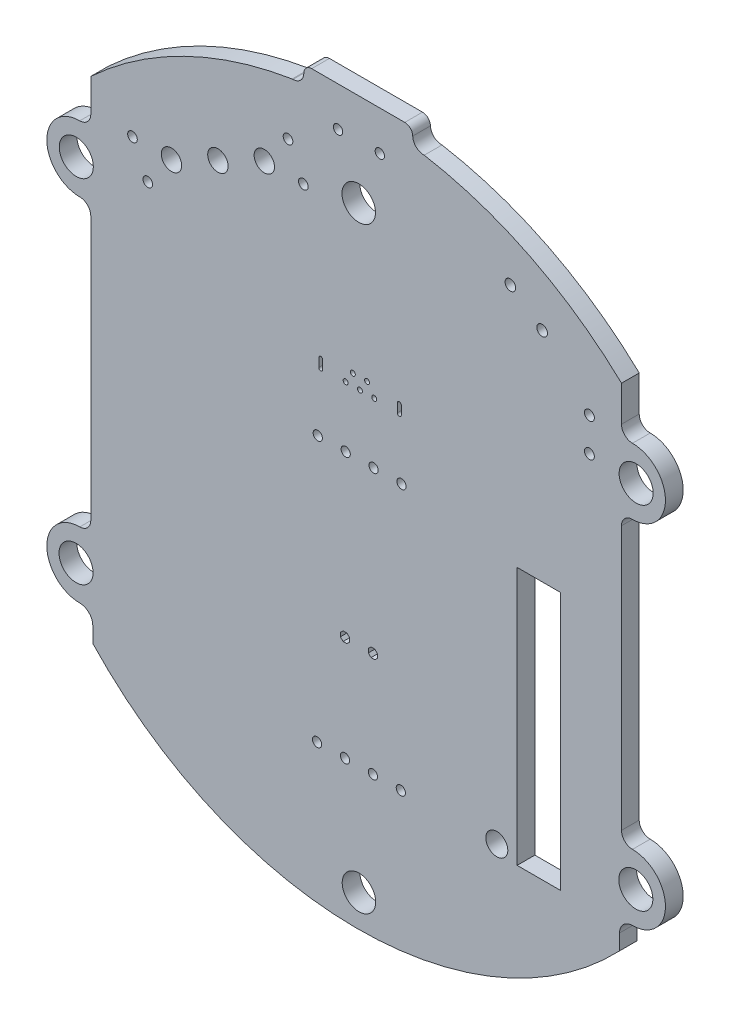
SolidWorks part; units mm, degrees
ref_plane "Front Plane" through (0, 0, 0) normal (0, 0, 1) x (1, 0, 0)
ref_plane "Top Plane" through (0, 0, 0) normal (0, 1, 0) x (1, 0, 0)
ref_plane "Right Plane" through (0, 0, 0) normal (1, 0, 0) x (0, 0, -1)
sketch "Model" plane through (0, 0, 0) normal (0, 0, 1) x (1, 0, 0)
  line L1 (-3.0387, 14.0018) -> (-3.0387, 13.2168) construction
  line L2 (-2.8588, 14.0018) -> (-2.8588, 13.2168)
  line L3 (4.1113, 14.0018) -> (4.1113, 13.2168) construction
  line L4 (4.2912, 14.0018) -> (4.2912, 13.2168)
  line L5 (3.9314, 14.0018) -> (3.9314, 13.2168)
  line L6 (-3.2186, 14.0018) -> (-3.2186, 13.2168)
  line L18 (2.1284, -6.6742) -> (2.1284, -7.0215)
  line L19 (2.1284, -7.0215) -> (1.883, -7.2669)
  line L20 (1.883, -7.2669) -> (1.5356, -7.2669)
  line L21 (1.5356, -7.2669) -> (1.2902, -7.0215)
  line L22 (1.2902, -7.0215) -> (1.2902, -6.6742)
  line L23 (1.2902, -6.6742) -> (1.5356, -6.4287)
  line L24 (1.5356, -6.4287) -> (1.883, -6.4287)
  line L25 (1.883, -6.4287) -> (2.1284, -6.6742)
  line L26 (2.1284, -6.6742) -> (2.1284, -7.0215)
  line L27 (2.1284, -6.6742) -> (2.1284, -7.0215)
  line L28 (2.1284, -7.0215) -> (1.883, -7.2669)
  line L29 (1.883, -7.2669) -> (1.5356, -7.2669)
  line L30 (1.5356, -7.2669) -> (1.2902, -7.0215)
  line L31 (1.2902, -7.0215) -> (1.2902, -6.6742)
  line L32 (1.2902, -6.6742) -> (1.5356, -6.4287)
  line L33 (1.5356, -6.4287) -> (1.883, -6.4287)
  line L34 (1.883, -6.4287) -> (2.1284, -6.6742)
  line L35 (2.1284, -6.6742) -> (2.1284, -7.0215)
  line L36 (-0.4116, -6.6742) -> (-0.4116, -7.0215)
  line L37 (-0.4116, -7.0215) -> (-0.657, -7.2669)
  line L38 (-0.657, -7.2669) -> (-1.0044, -7.2669)
  line L39 (-1.0044, -7.2669) -> (-1.2498, -7.0215)
  line L40 (-1.2498, -7.0215) -> (-1.2498, -6.6742)
  line L41 (-1.2498, -6.6742) -> (-1.0044, -6.4287)
  line L42 (-1.0044, -6.4287) -> (-0.657, -6.4287)
  line L43 (-0.657, -6.4287) -> (-0.4116, -6.6742)
  line L44 (-0.4116, -6.6742) -> (-0.4116, -7.0215)
  line L45 (-0.4116, -6.6742) -> (-0.4116, -7.0215)
  line L46 (-0.4116, -7.0215) -> (-0.657, -7.2669)
  line L47 (-0.657, -7.2669) -> (-1.0044, -7.2669)
  line L48 (-1.0044, -7.2669) -> (-1.2498, -7.0215)
  line L49 (-1.2498, -7.0215) -> (-1.2498, -6.6742)
  line L50 (-1.2498, -6.6742) -> (-1.0044, -6.4287)
  line L51 (-1.0044, -6.4287) -> (-0.657, -6.4287)
  line L52 (-0.657, -6.4287) -> (-0.4116, -6.6742)
  line L53 (-0.4116, -6.6742) -> (-0.4116, -7.0215)
  line L73 (14.8323, 6.4867) -> (18.7693, 6.4867)
  line L74 (14.8323, 6.4867) -> (14.8323, -16.9913)
  line L75 (14.8323, -16.9913) -> (18.7693, -16.9913)
  line L76 (18.7693, 6.4867) -> (18.7693, -16.9913)
  line L196 (-23.7797, -18.8098) -> (-23.7797, -17.3988)
  line L197 (-23.9607, -9.2178) -> (-23.9607, 14.7822)
  line L198 (-23.9607, 22.7822) -> (-23.9607, 25.7822)
  line L199 (24.1467, -19.0764) -> (24.1453, -17.6648)
  line L200 (24.3263, -9.4838) -> (24.3263, 14.5162)
  line L201 (24.3263, 22.5162) -> (24.3293, 25.7522)
  line L202 (-5.6407, 34.7422) -> (-5.5607, 34.7422)
  line L203 (4.6093, 36.4422) -> (-3.8607, 36.4422)
  circle A0 centre (-3.3707, -16.3728) radius 0.4191
  circle A1 centre (-3.3707, -16.3728) radius 0.4191
  circle A2 centre (-0.8307, -16.3728) radius 0.4191
  circle A3 centre (-0.8307, -16.3728) radius 0.4191
  circle A4 centre (1.7093, -16.3728) radius 0.4191
  circle A5 centre (1.7093, -16.3728) radius 0.4191
  circle A6 centre (4.2493, -16.3728) radius 0.4191
  circle A7 centre (4.2493, -16.3728) radius 0.4191
  circle A9 centre (4.3128, 7.8047) radius 0.4191
  circle A11 centre (1.7728, 7.8047) radius 0.4191
  circle A13 centre (-0.7672, 7.8047) radius 0.4191
  circle A15 centre (-3.3072, 7.8047) radius 0.4191
  circle A16 centre (0.5301, 13.3118) radius 0.227
  circle A17 centre (0.5301, 13.3118) radius 0.227
  circle A18 centre (-0.1199, 14.3118) radius 0.227
  circle A19 centre (-0.1199, 14.3118) radius 0.227
  circle A20 centre (1.8301, 13.3118) radius 0.227
  circle A21 centre (1.8301, 13.3118) radius 0.227
  circle A22 centre (1.1801, 14.3118) radius 0.227
  circle A23 centre (1.1801, 14.3118) radius 0.227
  circle A24 centre (-0.7699, 13.3118) radius 0.227
  circle A25 centre (-0.7699, 13.3118) radius 0.227
  circle A26 centre (14.215, 28.4322) radius 0.4827
  circle A27 centre (-20.1687, 22.9182) radius 0.4382
  circle A28 centre (17.1073, 26.3034) radius 0.4827
  circle A29 centre (-18.7769, 20.0645) radius 0.4381
  arc A30 (4.2912, 14.0018) -> (3.9314, 14.0018) centre (4.1113, 14.0018) ccw
  circle A31 centre (-6.0145, 29.8217) radius 0.4382
  arc A32 (3.9314, 13.2168) -> (4.2912, 13.2168) centre (4.1113, 13.2168) ccw
  circle A33 centre (-4.6227, 26.968) radius 0.4381
  arc A34 (-2.8588, 14.0018) -> (-3.2186, 14.0018) centre (-3.0387, 14.0018) ccw
  circle A35 centre (-16.6191, 22.8832) radius 0.9271
  arc A36 (-3.2186, 13.2168) -> (-2.8588, 13.2168) centre (-3.0387, 13.2168) ccw
  circle A37 centre (-12.3957, 24.9431) radius 0.9271
  circle A39 centre (-8.1722, 27.003) radius 0.9271
  arc A40 (-23.7797, -18.8098) -> (24.1467, -19.0764) centre (0.3098, 3.7681) ccw
  arc A41 (-23.7797, -17.3988) -> (-24.9607, -16.2178) centre (-24.9607, -17.3988) ccw
  arc A42 (-27.9607, -13.2178) -> (-24.9607, -16.2178) centre (-24.9607, -13.2178) ccw
  arc A43 (-24.9607, -10.2178) -> (-27.9607, -13.2178) centre (-24.9607, -13.2178) ccw
  arc A44 (-24.9607, -10.2178) -> (-23.9607, -9.2178) centre (-24.9607, -9.2178) ccw
  arc A45 (-23.9607, 14.7822) -> (-24.9607, 15.7822) centre (-24.9607, 14.7822) ccw
  arc A46 (-27.9607, 18.7822) -> (-24.9607, 15.7822) centre (-24.9607, 18.7822) ccw
  arc A47 (-24.9607, 21.7822) -> (-27.9607, 18.7822) centre (-24.9607, 18.7822) ccw
  arc A48 (-24.9607, 21.7822) -> (-23.9607, 22.7822) centre (-24.9607, 22.7822) ccw
  arc A49 (25.3263, -16.4838) -> (24.1453, -17.6648) centre (25.3263, -17.6648) ccw
  arc A50 (25.3263, -16.4838) -> (28.3263, -13.4838) centre (25.3263, -13.4838) ccw
  arc A51 (28.3263, -13.4838) -> (25.3263, -10.4838) centre (25.3263, -13.4838) ccw
  arc A52 (24.3263, -9.4838) -> (25.3263, -10.4838) centre (25.3263, -9.4838) ccw
  arc A53 (25.3263, 15.5162) -> (24.3263, 14.5162) centre (25.3263, 14.5162) ccw
  arc A54 (25.3263, 15.5162) -> (28.3263, 18.5162) centre (25.3263, 18.5162) ccw
  arc A55 (28.3263, 18.5162) -> (25.3263, 21.5162) centre (25.3263, 18.5162) ccw
  arc A56 (24.3263, 22.5162) -> (25.3263, 21.5162) centre (25.3263, 22.5162) ccw
  arc A57 (-5.6407, 34.7422) -> (-23.9607, 25.7822) centre (0, 0) ccw
  arc A58 (24.3293, 25.7522) -> (6.3793, 34.7422) centre (0.504, 0.5961) ccw
  arc A59 (-5.5607, 34.7422) -> (-4.5807, 35.7222) centre (-5.5607, 35.7222) ccw
  arc A60 (-3.8607, 36.4422) -> (-4.5807, 35.7222) centre (-3.8607, 35.7222) ccw
  arc A61 (5.3293, 35.7222) -> (4.6093, 36.4422) centre (4.6093, 35.7222) ccw
  arc A62 (5.3293, 35.7222) -> (6.3793, 34.7422) centre (6.3443, 35.7572) ccw
  circle A63 centre (2.3393, 32.8522) radius 0.425
  circle A64 centre (-1.4607, 32.8522) radius 0.425
  circle A65 centre (21.4093, 21.7702) radius 0.45
  circle A66 centre (21.4093, 18.7342) radius 0.45
  circle A319 centre (0.4193, 27.9938) radius 1.524
  circle A320 centre (-25.2807, 18.7838) radius 1.55
  circle A321 centre (-25.3007, -13.2262) radius 1.55
  circle A322 centre (0.4393, -26.3162) radius 1.524
  circle A323 centre (25.6293, -13.4862) radius 1.55
  circle A324 centre (25.6593, 18.5238) radius 1.55
  circle A325 centre (12.9821, -16.2382) radius 1
  point P52 (-3.0387, 13.6093)
  point P58 (4.1113, 13.6093)
extrude "Boss-Extrude1" add sketch "Model" along normal blind 1.6129 contours A62 A61 L203 A60 A59 L202 A57 L198 A48 A47 A46 A45 L197 A44 A43 A42 A41 L196 A40 L199 A49 A50 A51 A52 L200 A53 A54 A55 A56 L201 A58 A325 A324 A323 A322 A321 A320 A319 A66 A65 A64
